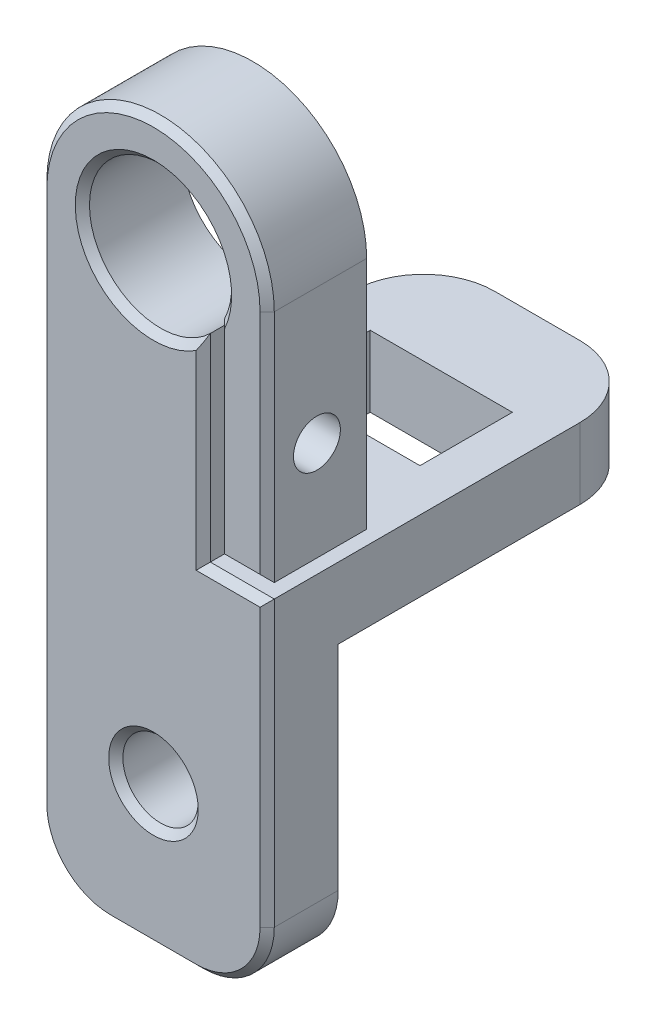
SolidWorks part; units mm, degrees
ref_plane "Plano frontal" through (0, 0, 0) normal (0, 0, 1) x (1, 0, 0)
ref_plane "Plano superior" through (0, 0, 0) normal (0, 1, 0) x (1, 0, 0)
ref_plane "Plano direito" through (0, 0, 0) normal (1, 0, 0) x (0, 0, -1)
sketch "Esboço1" plane through (0, 0, 0) normal (0, 0, 1) x (1, 0, 0)
  line L1 (7.983, 0.0159) -> (7.983, -37.4841)
  line L13 (-8.017, 0.0159) -> (-8.017, -37.4841)
  line L15 (2.983, -42.4841) -> (-3.017, -42.4841)
  circle A0 centre (-0.017, 0.0159) radius 5
  arc A2 (7.983, -37.4841) -> (2.983, -42.4841) centre (2.983, -37.4841) cw
  arc A3 (-3.017, -42.4841) -> (-8.017, -37.4841) centre (-3.017, -37.4841) cw
  arc A4 (7.983, 0.0159) -> (-8.017, 0.0159) centre (-0.017, 0.0159) ccw
  circle A5 centre (-0.017, -32.4841) radius 2.65
  point P16 (-0.017, -42.4841)
  dimension "D2" = 8
  dimension "D3" = 10
  dimension "D10" = 5.3
  dimension "D11" = 5
  dimension "D12" = 5
  dimension "D1" = 37.5
  dimension "D13" = 6
  dimension "D14" = 16
  dimension "D15" = 8
  dimension "D16" = 10
extrude "Ressalto-extrusão3" add sketch "Esboço1" along normal blind 7
sketch "Esboço3" plane through (0, -42.4841, 0) normal (0, -1, 0) x (1, 0, 0)
  line L0 (-8.017, 7) -> (-8.017, 0) construction
  line L1 (7.983, 0) -> (-8.017, 0)
  line L2 (7.983, 0) -> (7.983, -15)
  line L3 (2.983, -20) -> (-3.017, -20)
  line L4 (-8.017, 0) -> (-8.017, -15)
  line L6 (4.983, -13.25) -> (-5.017, -13.25)
  line L7 (4.983, -13.25) -> (4.983, -6.75)
  line L8 (4.983, -6.75) -> (-5.017, -6.75)
  line L9 (-5.017, -13.25) -> (-5.017, -6.75)
  arc A0 (7.983, -15) -> (2.983, -20) centre (2.983, -15) cw
  arc A1 (-3.017, -20) -> (-8.017, -15) centre (-3.017, -15) cw
  point P11 (-0.017, -13.25)
  point P12 (-0.017, -20)
  dimension "D5" = 5
  dimension "D1" = 20
  dimension "D2" = 6.75
  dimension "D3" = 6.5
  dimension "D4" = 10
extrude "Ressalto-extrusão4" add sketch "Esboço3" against normal blind 5 from offset 20 offset against normal yes
sketch "Esboço5" plane through (0, 0, 0) normal (0, 0, -1) x (-1, 0, 0)
  line L0 (-4.483, -2.1635) -> (-4.483, -16.4841)
  line L1 (-4.483, -16.4841) -> (-7.983, -16.4841)
  line L2 (-7.983, 0.0159) -> (-7.983, -17.4841) construction
  line L3 (-7.983, -16.4841) -> (-7.983, -17.4841)
  line L4 (-7.983, -17.4841) -> (-3.483, -17.4841)
  line L5 (-3.483, -17.4841) -> (-3.483, -3.5548)
  circle A1 centre (0.017, 0.0159) radius 5 construction
  arc A2 (-4.483, -2.1635) -> (-3.483, -3.5548) centre (0.017, 0.0159) ccw
  dimension "D1" = 1
  dimension "D2" = 1
  dimension "D3" = 3.5
extrude "Corte-extrusão2" cut sketch "Esboço5" against normal through all
sketch "Esboço6" plane through (7.983, 0, 0) normal (1, 0, 0) x (0, 0, -1)
  line L0 (-7, -16.4841) -> (0, -16.4841) construction
  line L1 (-7, -17.4841) -> (0, -17.4841) construction
  circle A0 centre (-3.5, -9.4841) radius 1.65
  point P5 (-3.5, -16.4841)
  dimension "D1" = 3.3
  dimension "D2" = 8
extrude "Corte-extrusão3" cut sketch "Esboço6" against normal through all
sketch "Esboço7" plane through (-8.017, 0, 0) normal (1, 0, 0) x (0, 0, -1)
  line L1 (-6.3, -7.8675) -> (-6.3, -11.1007)
  line L2 (-6.3, -11.1007) -> (-3.5, -12.7173)
  line L3 (-3.5, -12.7173) -> (-0.7, -11.1007)
  line L4 (-0.7, -11.1007) -> (-0.7, -7.8675)
  line L5 (-0.7, -7.8675) -> (-3.5, -6.2509)
  line L6 (-3.5, -6.2509) -> (-6.3, -7.8675)
  line L7 (-7, 0.0159) -> (-7, -37.4841) construction
  circle A0 centre (-3.5, -9.4841) radius 2.8 construction
  dimension "D1" = 5.6
extrude "Corte-extrusão4" cut sketch "Esboço7" along normal blind 4
chamfer "Chanfro1" distance 2.5 angle 45 1 edges at (-2.267, -17.4841, 0)
sketch "Esboço4" plane through (0, 0, 0) normal (0, 0, -1) x (-1, 0, 0)
  line L0 (-2.983, -42.4841) -> (3.017, -42.4841) construction
  line L1 (-7.983, -22.4841) -> (-7.983, -37.4841) construction
  line L2 (-7.983, -22.4841) -> (8.017, -22.4841) construction
  line L3 (-2.983, -42.4841) -> (3.017, -42.4841)
  line L4 (-7.983, -22.4841) -> (-7.983, -37.4841)
  line L5 (-7.983, -22.4841) -> (8.017, -22.4841)
  line L6 (8.017, -22.4841) -> (8.017, -37.4841) construction
  line L7 (8.017, -22.4841) -> (8.017, -37.4841)
  arc A0 (3.017, -42.4841) -> (8.017, -37.4841) centre (3.017, -37.4841) ccw construction
  arc A1 (-7.983, -37.4841) -> (-2.983, -42.4841) centre (-2.983, -37.4841) ccw construction
  arc A2 (3.017, -42.4841) -> (8.017, -37.4841) centre (3.017, -37.4841) ccw
  arc A3 (-7.983, -37.4841) -> (-2.983, -42.4841) centre (-2.983, -37.4841) ccw
extrude "Corte-extrusão1" cut sketch "Esboço4" against normal blind 2
chamfer "Chanfro2" distance 0.5 angle 45 12 edges at (2.633, -32.4841, 7) (4.483, -9.3238, 7) (-4.0771, 2.9341, 7) (3.483, -10.5195, 7) (5.733, -17.4841, 7) (7.983, -27.4841, 7) (6.5185, -41.0196, 7) (-0.017, -42.4841, 7) (-6.5526, -41.0196, 7) (-8.017, -18.7341, 7) (-0.017, 8.0159, 7) (6.233, -16.4841, 7)
